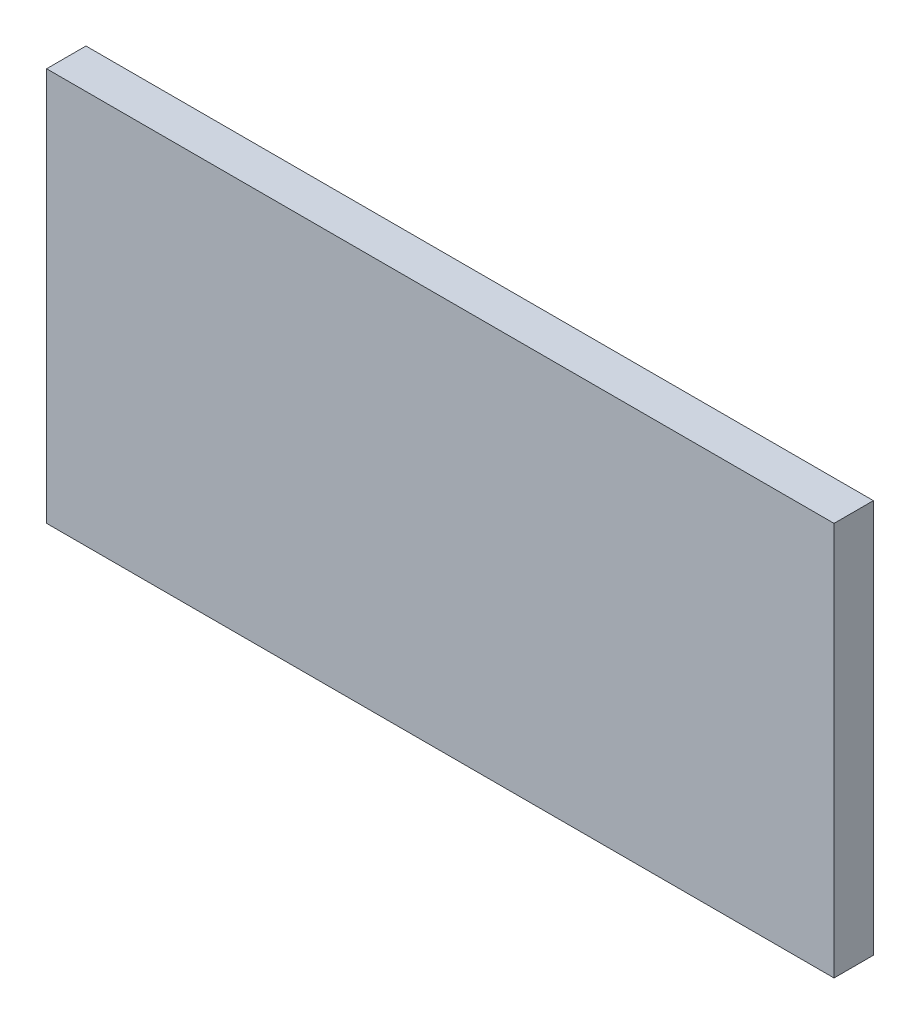
SolidWorks part; units mm, degrees
ref_plane "前视基准面" through (0, 0, 0) normal (0, 0, 1) x (1, 0, 0)
ref_plane "上视基准面" through (0, 0, 0) normal (0, 1, 0) x (1, 0, 0)
ref_plane "右视基准面" through (0, 0, 0) normal (1, 0, 0) x (0, 0, -1)
sketch "草图1" plane through (0, 0, 0) normal (0, 0, 1) x (1, 0, 0)
  line L1 (-30, 15) -> (30, 15)
  line L2 (-30, 15) -> (-30, -15)
  line L3 (-30, -15) -> (30, -15)
  line L4 (30, 15) -> (30, -15)
  line L5 (-30, 15) -> (30, -15) construction
  line L6 (-30, -15) -> (30, 15) construction
  point P1 (0, 0)
  dimension "D1" = 60
  dimension "D2" = 30
extrude "凸台-拉伸1" add sketch "草图1" along normal blind 3
